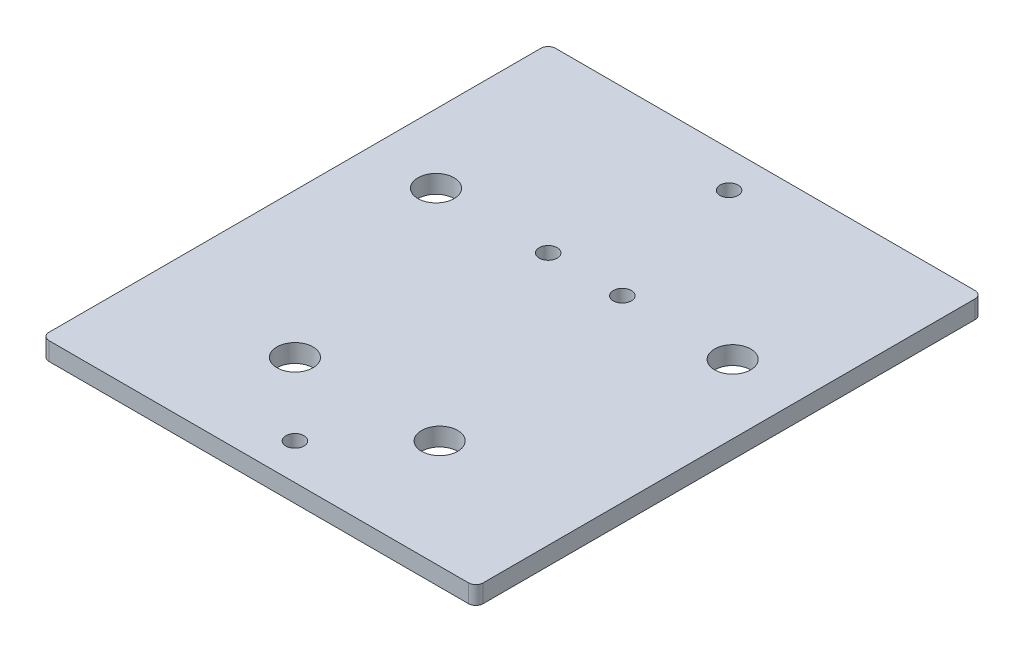
SolidWorks part; units mm, degrees
material "ABS"
ref_plane "Front Plane" through (0, 0, 0) normal (0, 0, 1) x (1, 0, 0)
ref_plane "Top Plane" through (0, 0, 0) normal (0, 1, 0) x (1, 0, 0)
ref_plane "Right Plane" through (0, 0, 0) normal (1, 0, 0) x (0, 0, -1)
sketch "Sketch1" plane through (0, 0, 0) normal (0, 1, 0) x (1, 0, 0)
  line L0 (76.2, 177.8) -> (76.2, 0) construction
  line L1 (0, 0) -> (152.4, 0)
  line L2 (0, 0) -> (0, 177.8)
  line L3 (0, 177.8) -> (152.4, 177.8)
  line L4 (152.4, 0) -> (152.4, 177.8)
  line L5 (24.13, 114.3) -> (128.27, 114.3) construction
  line L6 (101.6, 38.1) -> (50.8, 38.1) construction
  circle A0 centre (24.13, 114.3) radius 6.35
  circle A1 centre (128.27, 114.3) radius 6.35
  circle A2 centre (50.8, 38.1) radius 6.35
  circle A3 centre (101.6, 38.1) radius 6.35
  circle A4 centre (76.2, 165.1) radius 3.175
  circle A5 centre (76.2, 12.7) radius 3.175
  circle A6 centre (63.5, 114.3) radius 12.7 construction
  circle A7 centre (128.27, 114.3) radius 25.4 construction
  circle A8 centre (24.13, 114.3) radius 26.67 construction
  circle A9 centre (63.5, 114.3) radius 3.175
  circle A10 centre (89.535, 114.3) radius 13.335 construction
  circle A11 centre (89.535, 114.3) radius 3.175
  point P14 (76.2, 114.3)
  point P21 (76.2, 38.1)
  dimension "D3" = 12.7
  dimension "D11" = 6.35
  dimension "D8" = 25.4
  dimension "D12" = 50.8
  dimension "D13" = 6.35
  dimension "D14" = 26.67
  dimension "D1" = 177.8
  dimension "D2" = 152.4
  dimension "D4" = 104.14
  dimension "D5" = 12.7
  dimension "D6" = 38.1
  dimension "D7" = 50.8
  dimension "D9" = 76.2
  dimension "D10" = 12.7
extrude "Boss-Extrude1" add sketch "Sketch1" along normal blind 6.35
fillet "Fillet1" radius 2.54 4 edges at (0, 3.175, -177.8) (152.4, 3.175, -177.8) (152.4, 3.175, 0) (0, 3.175, 0)
